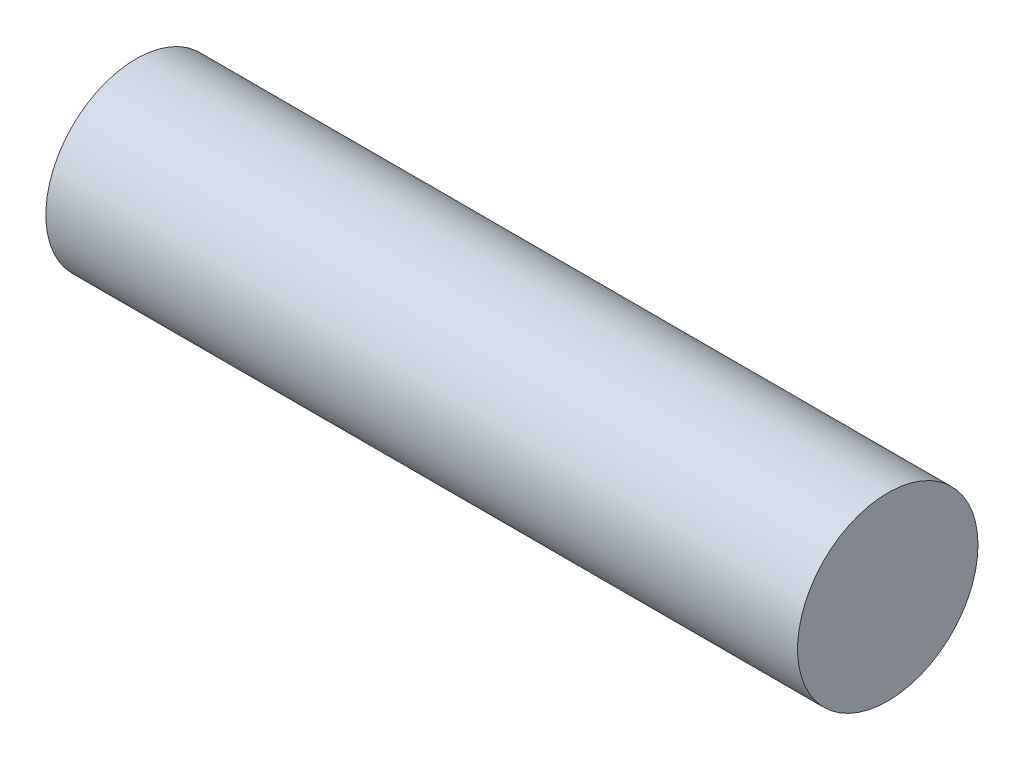
SolidWorks part; units mm, degrees
ref_plane "Alzado" through (0, 0, 0) normal (0, 0, 1) x (1, 0, 0)
ref_plane "Planta" through (0, 0, 0) normal (0, 1, 0) x (1, 0, 0)
ref_plane "Vista lateral" through (0, 0, 0) normal (1, 0, 0) x (0, 0, -1)
sketch "Croquis1" plane through (0, 0, 0) normal (1, 0, 0) x (0, 0, -1)
  circle A0 centre (0, 0) radius 3
extrude "Saliente-Extruir1" add sketch "Croquis1" along normal blind 25
